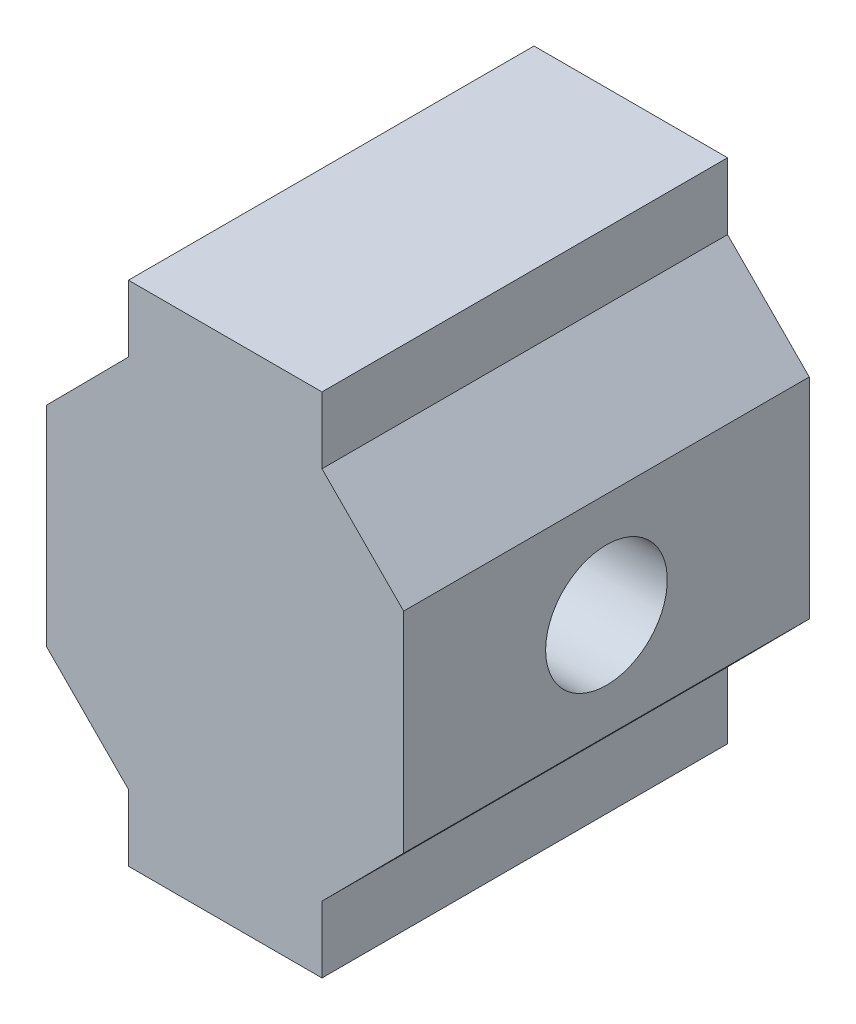
SolidWorks part; units mm, degrees
ref_plane "Front Plane" through (0, 0, 0) normal (0, 0, 1) x (1, 0, 0)
ref_plane "Top Plane" through (0, 0, 0) normal (0, 1, 0) x (1, 0, 0)
ref_plane "Right Plane" through (0, 0, 0) normal (1, 0, 0) x (0, 0, -1)
sketch "Sketch1" plane through (0, 0, 0) normal (0, 0, 1) x (1, 0, 0)
  line L28 (4.772, -12.514) -> (4.772, -9.2317)
  line L29 (4.772, -9.2317) -> (8.8, -5.1677)
  line L30 (8.8, 0) -> (8.8, -5.1677)
  line L31 (8.8, 0) -> (8.8, 5.1677)
  line L32 (4.772, 9.2317) -> (8.8, 5.1677)
  line L33 (4.772, 12.514) -> (4.772, 9.2317)
  line L34 (4.772, 12.514) -> (-4.772, 12.514)
  line L35 (-4.772, 12.514) -> (-4.772, 9.2317)
  line L36 (-4.772, 9.2317) -> (-8.8, 5.1677)
  line L37 (-8.8, 0) -> (-8.8, 5.1677)
  line L38 (-8.8, 0) -> (-8.8, -5.1677)
  line L39 (-4.772, -9.2317) -> (-8.8, -5.1677)
  line L40 (-4.772, -12.514) -> (-4.772, -9.2317)
  line L41 (4.772, -12.514) -> (-4.772, -12.514)
  point P2 (4.972, -11.014)
extrude "Boss-Extrude1" add sketch "Sketch1" along normal blind 20
sketch "Sketch2" plane through (0, 0, 0) normal (1, 0, 0) x (0, 0, -1)
  circle A0 centre (-10, 0) radius 3
extrude "Cut-Extrude1" cut sketch "Sketch2" against normal blind 20 and the other way blind 20
sketch "Sketch3" plane through (0, 0, 0) normal (0, 0, -1) x (-1, 0, 0)
  circle A0 centre (0, 0) radius 1.95
extrude "Cut-Extrude2" cut sketch "Sketch3" against normal blind 6
